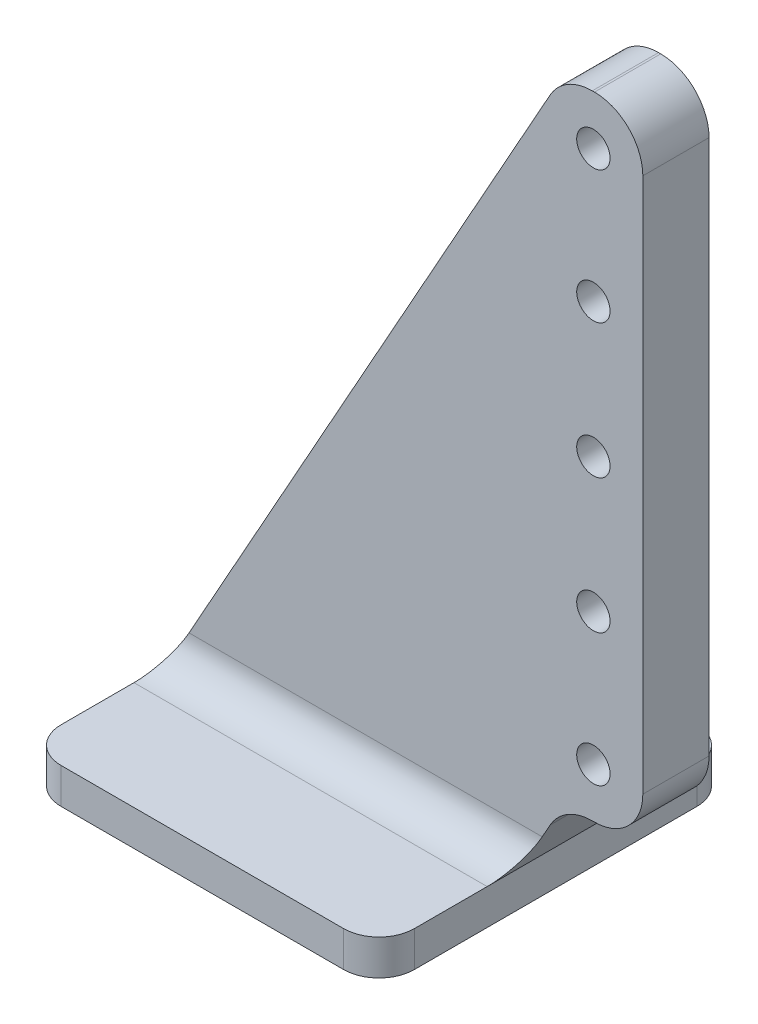
SolidWorks part; units mm, degrees
ref_plane "Front Plane" through (0, 0, 0) normal (0, 0, 1) x (1, 0, 0)
ref_plane "Top Plane" through (0, 0, 0) normal (0, 1, 0) x (1, 0, 0)
ref_plane "Right Plane" through (0, 0, 0) normal (1, 0, 0) x (0, 0, -1)
sketch "Sketch1" plane through (0, 0, 0) normal (0, 0, 1) x (1, 0, 0)
  line L0 (0, 0) -> (13.6924, 24.5094)
  line L1 (15.2101, 25.4) -> (15.2891, 25.4)
  line L2 (17.0276, 23.6615) -> (17.0276, 4.4055)
  line L3 (15.2891, 2.667) -> (15.2101, 2.667)
  line L4 (13.6924, 1.7764) -> (12.7, 0)
  line L5 (12.7, 0) -> (0, 0)
  line L6 (15.2496, 14.0335) -> (15.2496, 4.445) construction
  line L7 (15.2496, 4.445) -> (15.2496, 2.667) construction
  line L8 (15.2496, 25.4) -> (15.2496, 23.622) construction
  line L9 (15.2496, 23.622) -> (15.2496, 14.0335) construction
  circle A0 centre (15.2496, 4.445) radius 0.6
  circle A1 centre (15.2496, 23.622) radius 0.6
  circle A2 centre (15.2496, 14.0335) radius 0.6
  circle A3 centre (15.2496, 18.8595) radius 0.6
  circle A4 centre (15.2496, 9.2075) radius 0.6
  arc A5 (13.6924, 1.7764) -> (15.2101, 2.667) centre (15.2101, 0.9285) cw
  arc A6 (15.2891, 2.667) -> (17.0276, 4.4055) centre (15.2891, 4.4055) ccw
  arc A7 (17.0276, 23.6615) -> (15.2891, 25.4) centre (15.2891, 23.6615) ccw
  arc A8 (15.2101, 25.4) -> (13.6924, 24.5094) centre (15.2101, 23.6615) ccw
  point P17 (0, 0)
  point P28 (0, 0)
  point P29 (0, 0)
  point P30 (15.2496, 14.0335)
  point P31 (15.2496, 9.4394)
  point P32 (0, 0)
  point P33 (0, 0)
  point P34 (17.58, 17.1186)
  dimension "D1" = 25.4
  dimension "D6" = 1.2
  dimension "D7" = 4.826
  dimension "D2" = 1.778
  dimension "D3" = 12.7
  dimension "D4" = 2.667
  dimension "D5" = 1.778
  dimension "D8" = 4.826
extrude "Boss-Extrude1" add sketch "Sketch1" along normal blind 2.3813
sketch "Sketch2" plane through (0, 0, 0) normal (0, -1, 0) x (1, 0, 0)
  line L0 (0, 1.1906) -> (12.7, 1.1906) construction
  line L2 (12.7, 7.5406) -> (0, 7.5406)
  line L3 (12.7, 2.3813) -> (12.7, 0) construction
  line L4 (12.7, 7.5406) -> (12.7, -5.1594)
  line L5 (12.7, -5.1594) -> (0, -5.1594)
  line L6 (0, 7.5406) -> (0, -5.1594)
  line L7 (12.7, 7.5406) -> (0, -5.1594) construction
  line L8 (12.7, -5.1594) -> (0, 7.5406) construction
  line L10 (0, 2.3813) -> (0, 0) construction
  point P6 (6.35, 1.1906)
  dimension "D1" = 12.7
  dimension "D2" = 12.7
extrude "Boss-Extrude2" add sketch "Sketch2" along normal blind 1.2764
fillet "Fillet1" radius 1.27 6 edges at (12.7, -0.6382, 7.5406) (12.7, -0.6382, -5.1594) (0, -0.6382, -5.1594) (0, -0.6382, 7.5406)
